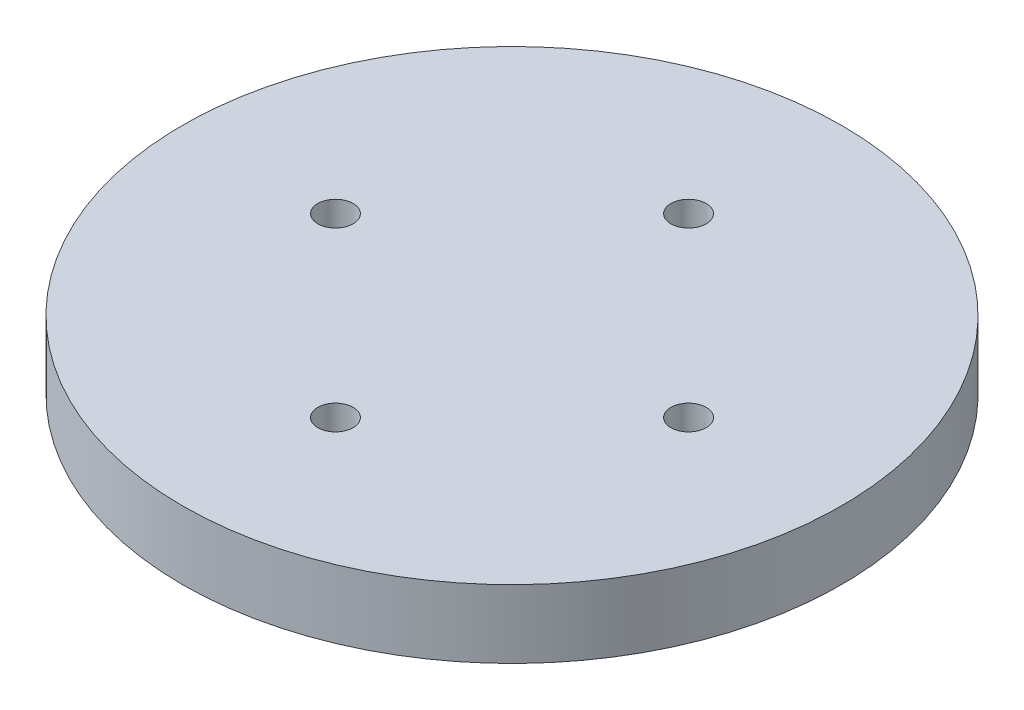
SolidWorks part; units mm, degrees
material "ABS"
ref_plane "Plan de face" through (0, 0, 0) normal (0, 0, 1) x (1, 0, 0)
ref_plane "Plan de dessus" through (0, 0, 0) normal (0, 1, 0) x (1, 0, 0)
ref_plane "Plan de droite" through (0, 0, 0) normal (1, 0, 0) x (0, 0, -1)
sketch "Esquisse1" plane through (0, 0, 0) normal (0, 1, 0) x (1, 0, 0)
  circle A0 centre (0, 0) radius 28
  circle A1 centre (0, 0) radius 15 construction
  circle A2 centre (0, 15) radius 1.5
  circle A3 centre (15, 0) radius 1.5
  circle A4 centre (0, -15) radius 1.5
  circle A5 centre (-15, 0) radius 1.5
  point P15 (0, 0)
  dimension "D1" = 56
  dimension "D2" = 30
  dimension "D3" = 3
  dimension "D4" = 4
extrude "Boss.-Extru.1" add sketch "Esquisse1" along normal blind 5.8
